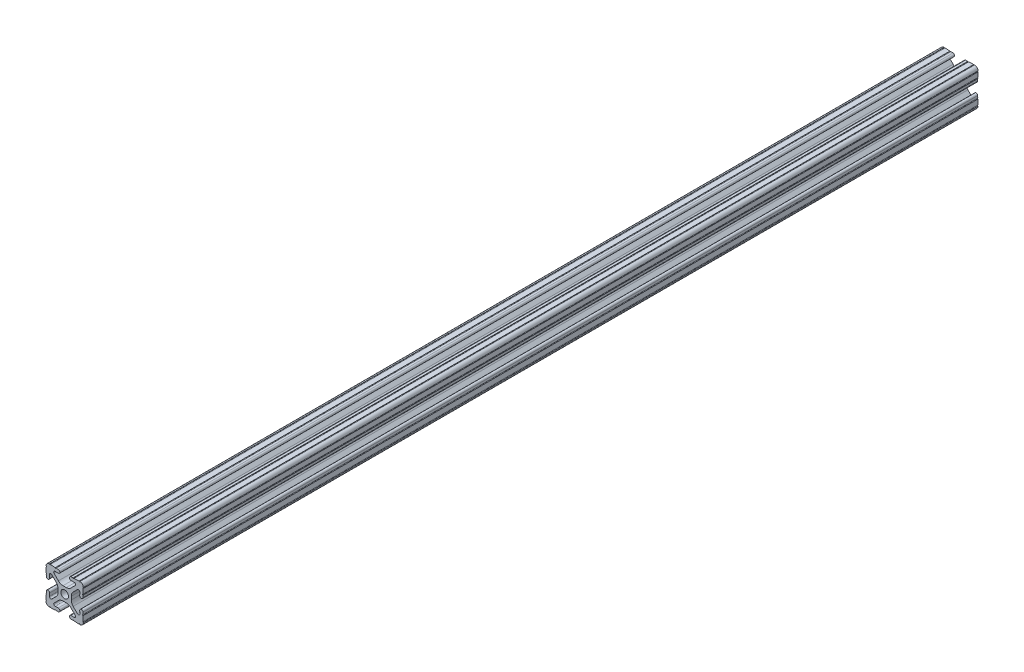
SolidWorks part; units mm, degrees
ref_plane "Front Plane" through (0, 0, 0) normal (0, 0, 1) x (1, 0, 0)
ref_plane "Top Plane" through (0, 0, 0) normal (0, 1, 0) x (1, 0, 0)
ref_plane "Right Plane" through (0, 0, 0) normal (1, 0, 0) x (0, 0, -1)
sketch "Sketch1" plane through (0, 0, 0) normal (0, 0, 1) x (1, 0, 0)
  line L0 (0, 12.7) -> (-12.7814, 12.7) construction
  line L1 (-4.5085, 0) -> (-4.5085, 2.9459)
  line L2 (-6.0437, 12.5461) -> (-10.0976, 12.6876) construction
  line L3 (-11.5616, 12.4229) -> (-4.3159, 12.1699) construction
  line L4 (-6.4364, 10.3486) -> (-6.3592, 12.5571) construction
  line L6 (-2.9459, 4.5085) -> (0, 4.5085)
  line L7 (0, 0) -> (0, 12.7) construction
  line L8 (0, 0) -> (-12.7814, 0) construction
  line L9 (0.7813, 0.7813) -> (-0.7813, -0.7813) construction
  line L10 (-2.9459, 4.5085) -> (-7.1484, 8.711)
  line L11 (-4.5085, 2.9459) -> (-8.711, 7.1484)
  line L13 (0, 0) -> (-12.7814, 12.7814) construction
  line L14 (-10.4131, 12.6987) -> (-4.3048, 12.4853)
  line L15 (-4.3048, 12.4853) -> (-4.382, 10.2769) construction
  line L16 (-4.382, 10.2769) -> (-6.4364, 10.3486)
  line L17 (-12.6987, 10.4131) -> (-12.4853, 4.3048)
  line L18 (-10.2769, 4.382) -> (-10.3486, 6.4364)
  circle A0 centre (0, 0) radius 2.6035
  arc A1 (-4.382, 10.2769) -> (-4.3048, 12.4853) centre (-4.3434, 11.3811) ccw
  arc A2 (-7.1484, 8.711) -> (-6.4364, 10.3486) centre (-6.4698, 9.3896) cw
  arc A3 (-8.711, 7.1484) -> (-10.3486, 6.4364) centre (-9.3896, 6.4698) ccw
  arc A4 (-10.2769, 4.382) -> (-12.4853, 4.3048) centre (-11.3811, 4.3434) cw
  arc A5 (-10.4131, 12.6987) -> (-12.6987, 10.4131) centre (-10.4902, 10.4902) ccw
  arc A6 (-10.4131, 12.6987) -> (-9.7821, 12.6766) centre (-10.0976, 12.6876) ccw
  arc A7 (-6.3592, 12.5571) -> (-5.7282, 12.5351) centre (-6.0437, 12.5461) ccw
  arc A8 (-12.5571, 6.3592) -> (-12.5351, 5.7282) centre (-12.5461, 6.0437) cw
  arc A9 (-12.6987, 10.4131) -> (-12.6766, 9.7821) centre (-12.6876, 10.0976) cw
  dimension "D1" = 5.207
  dimension "D5" = 14.859
  dimension "D9" = 2
  dimension "D2" = 25.4
  dimension "D12" = 0.6314
  dimension "D10" = 2.2098
  dimension "D3" = 9.017
  dimension "D4" = 9.017
  dimension "D6" = 25.4
  dimension "D7" = 6.477
  dimension "D8" = 2.2098
  dimension "D11" = 12.7
sketch "Sketch3" plane through (0, 0, 0) normal (0, 0, 1) x (1, 0, 0)
  line L0 (-2.9459, 4.5085) -> (0, 4.5085) construction
  line L1 (-2.9459, 4.5085) -> (-7.1484, 8.711) construction
  line L2 (-4.382, 10.2769) -> (-6.4364, 10.3486) construction
  line L3 (-10.4131, 12.6987) -> (-4.3048, 12.4853) construction
  line L4 (-4.5085, 0) -> (-4.5085, 2.9459) construction
  line L5 (-4.5085, 2.9459) -> (-8.711, 7.1484) construction
  line L6 (-10.2769, 4.382) -> (-10.3486, 6.4364) construction
  line L7 (-12.6987, 10.4131) -> (-12.4853, 4.3048) construction
  line L8 (-1.1153, 4.5085) -> (1.1153, 4.5085)
  line L9 (-4.2404, 5.803) -> (-7.1484, 8.711)
  line L10 (-4.382, 10.2769) -> (-6.4364, 10.3486)
  line L11 (-9.7821, 12.6766) -> (-6.3592, 12.5571)
  line L12 (-4.5085, -1.1153) -> (-4.5085, 1.1153)
  line L13 (-5.803, 4.2404) -> (-8.711, 7.1484)
  line L14 (-10.2769, 4.382) -> (-10.3486, 6.4364)
  line L15 (-12.6766, 9.7821) -> (-12.5571, 6.3592)
  line L16 (-5.7282, 12.5351) -> (-4.3048, 12.4853)
  line L17 (-12.5351, 5.7282) -> (-12.4853, 4.3048)
  line L18 (0, 0) -> (0, 12.7) construction
  line L19 (0, 0) -> (-12.7814, 0) construction
  line L20 (12.5351, 5.7282) -> (12.4853, 4.3048)
  line L21 (5.7282, 12.5351) -> (4.3048, 12.4853)
  line L22 (12.6766, 9.7821) -> (12.5571, 6.3592)
  line L23 (10.2769, 4.382) -> (10.3486, 6.4364)
  line L24 (5.803, 4.2404) -> (8.711, 7.1484)
  line L25 (4.5085, -1.1153) -> (4.5085, 1.1153)
  line L26 (9.7821, 12.6766) -> (6.3592, 12.5571)
  line L27 (4.382, 10.2769) -> (6.4364, 10.3486)
  line L28 (4.2404, 5.803) -> (7.1484, 8.711)
  line L29 (4.2404, -5.803) -> (7.1484, -8.711)
  line L30 (4.382, -10.2769) -> (6.4364, -10.3486)
  line L31 (9.7821, -12.6766) -> (6.3592, -12.5571)
  line L32 (5.803, -4.2404) -> (8.711, -7.1484)
  line L33 (10.2769, -4.382) -> (10.3486, -6.4364)
  line L34 (12.6766, -9.7821) -> (12.5571, -6.3592)
  line L35 (5.7282, -12.5351) -> (4.3048, -12.4853)
  line L36 (12.5351, -5.7282) -> (12.4853, -4.3048)
  line L37 (-12.5351, -5.7282) -> (-12.4853, -4.3048)
  line L38 (-5.7282, -12.5351) -> (-4.3048, -12.4853)
  line L39 (-12.6766, -9.7821) -> (-12.5571, -6.3592)
  line L40 (-10.2769, -4.382) -> (-10.3486, -6.4364)
  line L41 (-5.803, -4.2404) -> (-8.711, -7.1484)
  line L42 (-9.7821, -12.6766) -> (-6.3592, -12.5571)
  line L43 (-4.382, -10.2769) -> (-6.4364, -10.3486)
  line L44 (-4.2404, -5.803) -> (-7.1484, -8.711)
  line L45 (-1.1153, -4.5085) -> (1.1153, -4.5085)
  arc A0 (-10.4131, 12.6987) -> (-9.7821, 12.6766) centre (-10.0976, 12.6876) ccw construction
  arc A1 (-6.4364, 10.3486) -> (-7.1484, 8.711) centre (-6.4698, 9.3896) ccw construction
  arc A2 (-4.382, 10.2769) -> (-4.3048, 12.4853) centre (-4.3434, 11.3811) ccw construction
  arc A3 (-8.711, 7.1484) -> (-10.3486, 6.4364) centre (-9.3896, 6.4698) ccw construction
  arc A4 (-12.4853, 4.3048) -> (-10.2769, 4.382) centre (-11.3811, 4.3434) ccw construction
  arc A5 (-6.3592, 12.5571) -> (-5.7282, 12.5351) centre (-6.0437, 12.5461) ccw construction
  arc A6 (-10.4131, 12.6987) -> (-12.6987, 10.4131) centre (-10.4902, 10.4902) ccw construction
  arc A7 (-12.6766, 9.7821) -> (-12.6987, 10.4131) centre (-12.6876, 10.0976) ccw construction
  arc A8 (-12.5351, 5.7282) -> (-12.5571, 6.3592) centre (-12.5461, 6.0437) ccw construction
  arc A9 (-10.4131, 12.6987) -> (-9.7821, 12.6766) centre (-10.0976, 12.6876) ccw
  arc A10 (-6.4364, 10.3486) -> (-7.1484, 8.711) centre (-6.4698, 9.3896) ccw
  arc A11 (-4.382, 10.2769) -> (-4.3048, 12.4853) centre (-4.3434, 11.3811) ccw
  arc A12 (-8.711, 7.1484) -> (-10.3486, 6.4364) centre (-9.3896, 6.4698) ccw
  arc A13 (-12.4853, 4.3048) -> (-10.2769, 4.382) centre (-11.3811, 4.3434) ccw
  arc A14 (-6.3592, 12.5571) -> (-5.7282, 12.5351) centre (-6.0437, 12.5461) ccw
  arc A15 (-10.4131, 12.6987) -> (-12.6987, 10.4131) centre (-10.4902, 10.4902) ccw
  arc A16 (-12.6766, 9.7821) -> (-12.6987, 10.4131) centre (-12.6876, 10.0976) ccw
  arc A17 (-12.5351, 5.7282) -> (-12.5571, 6.3592) centre (-12.5461, 6.0437) ccw
  arc A18 (-1.1153, 4.5085) -> (-4.2404, 5.803) centre (-1.1153, 8.9281) cw
  arc A19 (4.5085, 1.1153) -> (5.803, 4.2404) centre (8.9281, 1.1153) cw
  arc A20 (1.1153, 4.5085) -> (4.2404, 5.803) centre (1.1153, 8.9281) ccw
  arc A21 (-4.5085, 1.1153) -> (-5.803, 4.2404) centre (-8.9281, 1.1153) ccw
  arc A22 (12.5351, 5.7282) -> (12.5571, 6.3592) centre (12.5461, 6.0437) cw
  arc A23 (12.6766, 9.7821) -> (12.6987, 10.4131) centre (12.6876, 10.0976) cw
  arc A24 (10.4131, 12.6987) -> (12.6987, 10.4131) centre (10.4902, 10.4902) cw
  arc A25 (6.3592, 12.5571) -> (5.7282, 12.5351) centre (6.0437, 12.5461) cw
  arc A26 (12.4853, 4.3048) -> (10.2769, 4.382) centre (11.3811, 4.3434) cw
  arc A27 (8.711, 7.1484) -> (10.3486, 6.4364) centre (9.3896, 6.4698) cw
  arc A28 (4.382, 10.2769) -> (4.3048, 12.4853) centre (4.3434, 11.3811) cw
  arc A29 (6.4364, 10.3486) -> (7.1484, 8.711) centre (6.4698, 9.3896) cw
  arc A30 (10.4131, 12.6987) -> (9.7821, 12.6766) centre (10.0976, 12.6876) cw
  arc A31 (10.4131, -12.6987) -> (9.7821, -12.6766) centre (10.0976, -12.6876) ccw
  arc A32 (6.4364, -10.3486) -> (7.1484, -8.711) centre (6.4698, -9.3896) ccw
  arc A33 (4.382, -10.2769) -> (4.3048, -12.4853) centre (4.3434, -11.3811) ccw
  arc A34 (8.711, -7.1484) -> (10.3486, -6.4364) centre (9.3896, -6.4698) ccw
  arc A35 (12.4853, -4.3048) -> (10.2769, -4.382) centre (11.3811, -4.3434) ccw
  arc A36 (6.3592, -12.5571) -> (5.7282, -12.5351) centre (6.0437, -12.5461) ccw
  arc A37 (10.4131, -12.6987) -> (12.6987, -10.4131) centre (10.4902, -10.4902) ccw
  arc A38 (12.6766, -9.7821) -> (12.6987, -10.4131) centre (12.6876, -10.0976) ccw
  arc A39 (12.5351, -5.7282) -> (12.5571, -6.3592) centre (12.5461, -6.0437) ccw
  arc A40 (-4.5085, -1.1153) -> (-5.803, -4.2404) centre (-8.9281, -1.1153) cw
  arc A41 (1.1153, -4.5085) -> (4.2404, -5.803) centre (1.1153, -8.9281) cw
  arc A42 (4.5085, -1.1153) -> (5.803, -4.2404) centre (8.9281, -1.1153) ccw
  arc A43 (-1.1153, -4.5085) -> (-4.2404, -5.803) centre (-1.1153, -8.9281) ccw
  arc A44 (-12.5351, -5.7282) -> (-12.5571, -6.3592) centre (-12.5461, -6.0437) cw
  arc A45 (-12.6766, -9.7821) -> (-12.6987, -10.4131) centre (-12.6876, -10.0976) cw
  arc A46 (-10.4131, -12.6987) -> (-12.6987, -10.4131) centre (-10.4902, -10.4902) cw
  arc A47 (-6.3592, -12.5571) -> (-5.7282, -12.5351) centre (-6.0437, -12.5461) cw
  arc A48 (-12.4853, -4.3048) -> (-10.2769, -4.382) centre (-11.3811, -4.3434) cw
  arc A49 (-8.711, -7.1484) -> (-10.3486, -6.4364) centre (-9.3896, -6.4698) cw
  arc A50 (-4.382, -10.2769) -> (-4.3048, -12.4853) centre (-4.3434, -11.3811) cw
  arc A51 (-6.4364, -10.3486) -> (-7.1484, -8.711) centre (-6.4698, -9.3896) cw
  arc A52 (-10.4131, -12.6987) -> (-9.7821, -12.6766) centre (-10.0976, -12.6876) cw
  circle A53 centre (0, 0) radius 2.6035 construction
  circle A54 centre (0, 0) radius 2.6035
  point P135 (4.5085, 0)
  dimension "D2" = 4.4196
extrude "Extrude1" add sketch "Sketch3" along normal mid plane 609.6
equation "\"D10@Sketch1\" = \"D8@Sketch1\""
equation "\"D11@Sketch1\" = \"D6@Sketch1\"/2"
equation "\"D12@Sketch1\" = \"D8@Sketch1\"/3.5"
equation "\"D2@Sketch3\" = \"D8@Sketch1\"*2"
